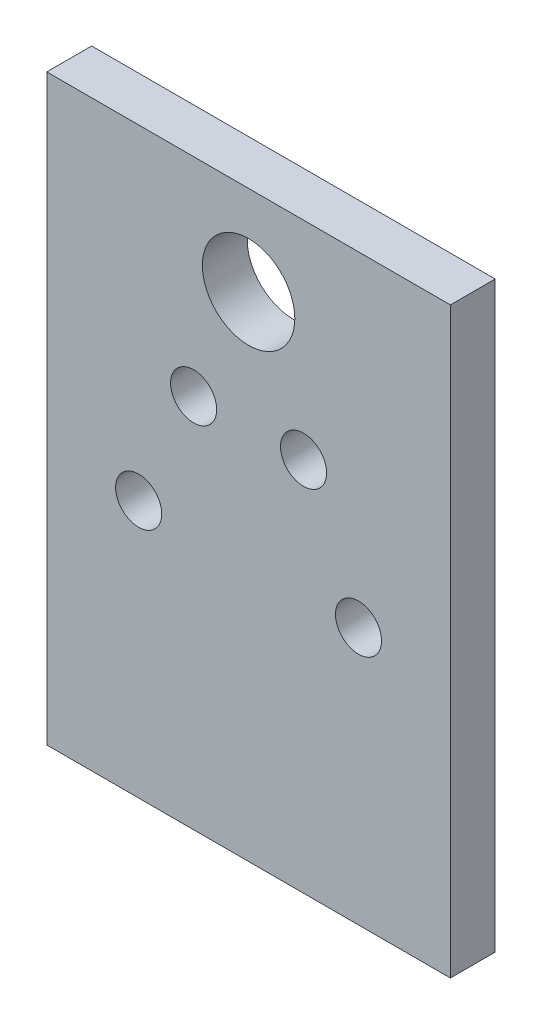
SolidWorks part; units mm, degrees
material "1060 Alloy"
ref_plane "Front Plane" through (0, 0, 0) normal (0, 0, 1) x (1, 0, 0)
ref_plane "Top Plane" through (0, 0, 0) normal (0, 1, 0) x (1, 0, 0)
ref_plane "Right Plane" through (0, 0, 0) normal (1, 0, 0) x (0, 0, -1)
sketch "Sketch1" plane through (0, 0, 0) normal (0, 0, 1) x (1, 0, 0)
  line L0 (0, 12.7) -> (0, 69.85) construction
  line L1 (-28.575, 12.7) -> (28.575, 12.7) construction
  line L2 (-28.575, 12.7) -> (-28.575, -12.7)
  line L3 (-28.575, -12.7) -> (28.575, -12.7)
  line L4 (28.575, 12.7) -> (28.575, -12.7)
  line L5 (0, -12.7) -> (0, 12.7) construction
  line L6 (-28.575, 0) -> (28.575, 0) construction
  line L7 (-28.575, 12.7) -> (28.575, 12.7) construction
  line L8 (-28.575, 12.7) -> (-28.575, 57.15)
  line L9 (-28.575, 57.15) -> (28.575, 57.15) construction
  line L10 (28.575, 12.7) -> (28.575, 57.15)
  line L11 (-28.575, 57.15) -> (28.575, 57.15) construction
  line L12 (-28.575, 57.15) -> (-28.575, 69.85)
  line L13 (-28.575, 69.85) -> (28.575, 69.85)
  line L14 (28.575, 57.15) -> (28.575, 69.85)
  line L15 (0, 57.15) -> (-21.1248, 26.9806) construction
  line L16 (0, 57.15) -> (-15.565, 23.7707) construction
  circle A0 centre (0, 57.15) radius 6.5481
  arc A1 (-21.1248, 26.9806) -> (21.1248, 26.9806) centre (0, 57.15) ccw construction
  arc A2 (-22.9969, 24.307) -> (22.9969, 24.307) centre (0, 57.15) ccw construction
  arc A3 (-19.2527, 29.6543) -> (19.2527, 29.6543) centre (0, 57.15) ccw construction
  arc A4 (-19.2527, 29.6543) -> (-22.9969, 24.307) centre (-21.1248, 26.9806) ccw construction
  arc A5 (22.9969, 24.307) -> (19.2527, 29.6543) centre (21.1248, 26.9806) ccw construction
  arc A6 (-10.5624, 42.0653) -> (10.5624, 42.0653) centre (0, 57.15) ccw construction
  arc A7 (-12.4345, 39.3917) -> (12.4345, 39.3917) centre (0, 57.15) ccw construction
  arc A8 (-8.6903, 44.7389) -> (8.6903, 44.7389) centre (0, 57.15) ccw construction
  arc A9 (-8.6903, 44.7389) -> (-12.4345, 39.3917) centre (-10.5624, 42.0653) ccw construction
  arc A10 (12.4345, 39.3917) -> (8.6903, 44.7389) centre (10.5624, 42.0653) ccw construction
  circle A11 centre (-7.7825, 40.4603) radius 3.2639
  circle A12 centre (-15.565, 23.7707) radius 3.2639
  circle A13 centre (7.7825, 40.4603) radius 3.2639
  circle A14 centre (15.565, 23.7707) radius 3.2639
  point P0 (0, 0)
  point P15 (0, 20.32)
  point P20 (0, 38.735)
  point P37 (0, 41.91)
  dimension "D5" = 13.0962
  dimension "D1" = 12.7
  dimension "D2" = 57.15
  dimension "D3" = 25.4
  dimension "D4" = 57.15
  dimension "D7" = 6.5278
  dimension "D8" = 7.62
  dimension "D9" = 6.5278
  dimension "D10" = 35
  dimension "D11" = 25
extrude "Boss-Extrude1" add sketch "Sketch1" along normal blind 6.35
